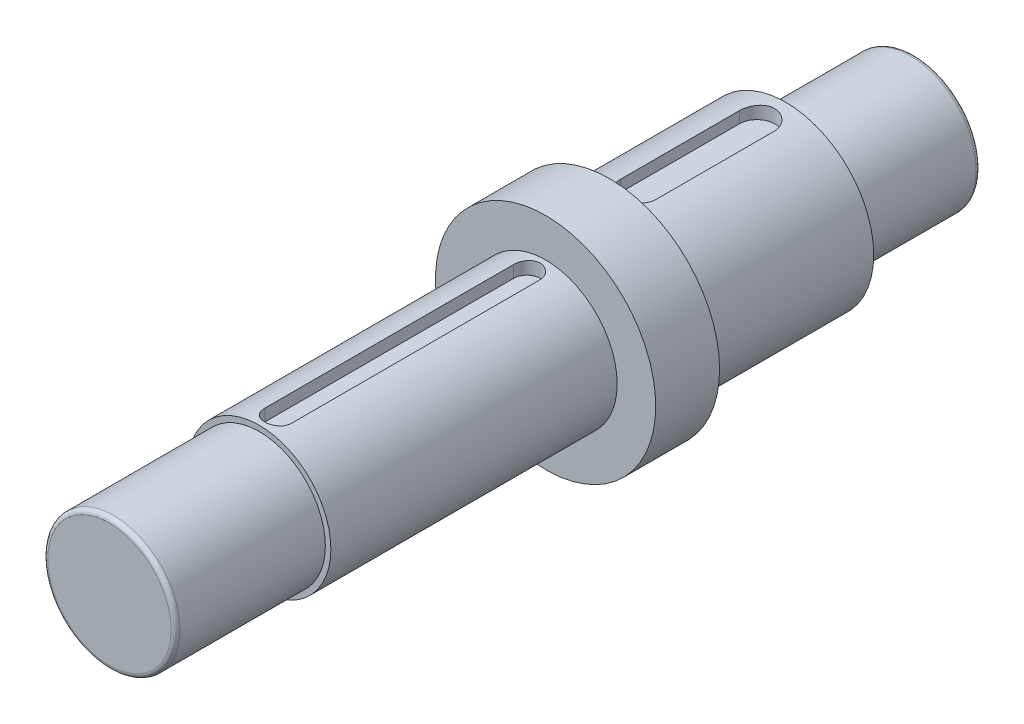
SolidWorks part; units mm, degrees
ref_plane "Front Plane" through (0, 0, 0) normal (0, 0, 1) x (1, 0, 0)
ref_plane "Top Plane" through (0, 0, 0) normal (0, 1, 0) x (1, 0, 0)
ref_plane "Right Plane" through (0, 0, 0) normal (1, 0, 0) x (0, 0, -1)
sketch "Sketch1" plane through (0, 0, 0) normal (1, 0, 0) x (0, 0, -1)
  line L0 (0, 0) -> (-365.5, 0)
  line L1 (-365.5, 0) -> (-365.5, 30)
  line L2 (-365.5, 30) -> (-297.5, 30)
  line L3 (-297.5, 30) -> (-297.5, 32.5)
  line L4 (-297.5, 32.5) -> (-167.5, 32.5)
  line L5 (-167.5, 32.5) -> (-167.5, 50)
  line L6 (-167.5, 50) -> (-138.5, 50)
  line L7 (-138.5, 50) -> (-138.5, 40)
  line L8 (-138.5, 40) -> (-58.5, 40)
  line L9 (-58.5, 40) -> (-58.5, 30)
  line L10 (-58.5, 30) -> (0, 30)
  line L11 (0, 30) -> (0, 0)
  line L12 (0, 0) -> (142.4942, 0) construction
  dimension "D1" = 68
  dimension "D2" = 130
  dimension "D3" = 29
  dimension "D4" = 80
  dimension "D5" = 58.5
  dimension "D6" = 60
  dimension "D7" = 80
  dimension "D8" = 100
  dimension "D9" = 65
  dimension "D10" = 60
revolve "Revolve1" add sketch "Sketch1" angle 360 about L12
fillet "Fillet1" radius 2 2 edges at (30, 0, 365.5) (30, 0, 0)
sketch "Sketch2" plane through (0, 0, 0) normal (0, 1, 0) x (1, 0, 0)
  line L0 (0, -71.5) -> (0, -125.5) construction
  line L1 (8, -71.5) -> (8, -125.5)
  line L2 (-8, -71.5) -> (-8, -125.5)
  line L3 (40, -58.5) -> (-40, -58.5) construction
  arc A0 (8, -71.5) -> (-8, -71.5) centre (0, -71.5) ccw
  arc A1 (-8, -125.5) -> (8, -125.5) centre (0, -125.5) ccw
  point P3 (0, -98.5)
  dimension "D1" = 8
  dimension "D2" = 40
  dimension "D3" = 54
extrude "Cut-Extrude1" cut sketch "Sketch2" along normal blind 10 from offset 34
sketch "Sketch3" plane through (0, 0, 0) normal (0, 1, 0) x (1, 0, 0)
  line L0 (0, -176) -> (0, -289) construction
  line L1 (6, -176) -> (6, -289)
  line L2 (-6, -176) -> (-6, -289)
  line L3 (-30, -297.5) -> (30, -297.5) construction
  arc A0 (6, -176) -> (-6, -176) centre (0, -176) ccw
  arc A1 (-6, -289) -> (6, -289) centre (0, -289) ccw
  point P3 (0, -232.5)
  dimension "D1" = 6
  dimension "D2" = 65
  dimension "D3" = 113
extrude "Cut-Extrude2" cut sketch "Sketch3" along normal blind 10 from offset 26.5
equation "\"D3@Sketch2\"=70-16"
equation "\"D3@Sketch3\"=125-12"
